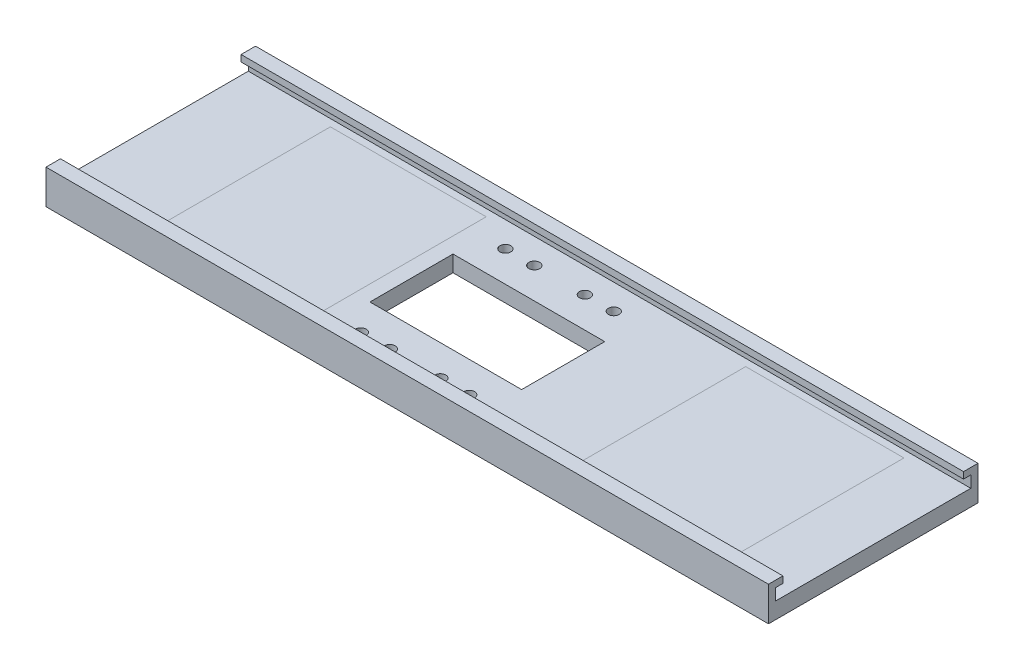
SolidWorks part; units mm, degrees
ref_plane "前视基准面" through (0, 0, 0) normal (0, 0, 1) x (1, 0, 0)
ref_plane "上视基准面" through (0, 0, 0) normal (0, 1, 0) x (1, 0, 0)
ref_plane "右视基准面" through (0, 0, 0) normal (1, 0, 0) x (0, 0, -1)
sketch "草图1" plane through (0, 0, 0) normal (1, 0, 0) x (0, 0, -1)
  line L0 (0, 28.6691) -> (0, -27.5601) construction
  line L1 (-29, 0) -> (29, 0)
  line L2 (29, 0) -> (29, 9.5)
  line L3 (29, 9.5) -> (25, 9.5)
  line L4 (25, 9.5) -> (25, 4.5)
  line L5 (25, 4.5) -> (-25, 4.5)
  line L6 (-29, 0) -> (-29, 9.5)
  line L7 (-29, 9.5) -> (-25, 9.5)
  line L8 (-25, 9.5) -> (-25, 4.5)
  point P10 (0, 0)
  point P13 (0, 4.5)
  dimension "D1" = 50
  dimension "D2" = 4.5
  dimension "D3" = 4
  dimension "D4" = 5
extrude "凸台-拉伸1" add sketch "草图1" along normal blind 180 and the other way blind 20
sketch "草图2" plane through (0, 4.5, 0) normal (0, 1, 0) x (1, 0, 0)
  line L0 (0, 0) -> (180, 0) construction
  line L1 (180, 25) -> (180, -25) construction
  line L2 (75, 10) -> (75, -10) construction
  line L5 (58.67, 10) -> (58.67, -10) construction
  line L8 (97.67, 10) -> (97.67, -10) construction
  line L9 (58.67, 10) -> (97.67, 10) construction
  line L10 (58.67, -10) -> (97.67, -10) construction
  line L20 (52.17, 11.5) -> (94.17, 11.5)
  line L21 (52.17, 11.5) -> (52.17, -11.5)
  line L22 (52.17, -11.5) -> (94.17, -11.5)
  line L23 (94.17, 11.5) -> (94.17, -11.5)
  line L24 (52.17, 11.5) -> (94.17, -11.5) construction
  line L25 (52.17, -11.5) -> (94.17, 11.5) construction
  circle A0 centre (90, 0) radius 3 construction
  point P6 (63.3128, 0)
  point P7 (73.17, 0)
  dimension "D1" = 6
  dimension "D2" = 31.33
  dimension "D3" = 39
  dimension "D4" = 10
  dimension "D5" = 10
  dimension "D6" = 23
  dimension "D7" = 42
extrude "切除-拉伸1" cut sketch "草图2" against normal through all
sketch "草图4" plane through (0, 4.5, 0) normal (0, 1, 0) x (1, 0, 0)
  line L1 (73.17, 25) -> (73.17, -25) construction
  line L2 (-20, 25) -> (180, 25) construction
  line L3 (-20, -25) -> (180, -25) construction
  line L7 (94.17, 11.5) -> (52.17, 11.5) construction
  line L8 (-20, 25) -> (180, 25) construction
  line L9 (-20, 0) -> (180, 0) construction
  line L10 (-20, 25) -> (-20, -25) construction
  line L11 (180, 25) -> (180, -25) construction
  circle A8 centre (66.17, 20) radius 1.5
  circle A9 centre (80.17, 20) radius 1.5
  circle A10 centre (88.17, 20) radius 1.5
  circle A11 centre (58.17, 20) radius 1.5
  circle A12 centre (88.17, -20) radius 1.5
  circle A13 centre (80.17, -20) radius 1.5
  circle A14 centre (66.17, -20) radius 1.5
  circle A15 centre (58.17, -20) radius 1.5
  point P13 (73.17, 11.5)
  dimension "D1" = 3
  dimension "D2" = 5
  dimension "D6" = 5
  dimension "D4" = 3
  dimension "D3" = 14
  dimension "D5" = 8
extrude "切除-拉伸2" cut sketch "草图4" against normal through all
ref_plane "基准面1" through (180, 0, 0) normal (1, 0, 0) x (0, 0, -1)
sketch "草图5" plane through (180, 0, 0) normal (1, 0, 0) x (0, 0, -1)
  line L1 (-25, 4.5) -> (-25, 9.5) construction
  line L3 (-25, 7.7) -> (-25, 5.5)
  line L8 (-25, 7.7) -> (-27, 7.7)
  line L9 (-27, 7.7) -> (-27, 5.5)
  line L10 (-27, 5.5) -> (-25, 5.5)
  line L11 (0, 10.1018) -> (0, 0) construction
  line L12 (25, 7.7) -> (25, 5.5)
  line L13 (27, 5.5) -> (25, 5.5)
  line L14 (27, 7.7) -> (27, 5.5)
  line L15 (25, 7.7) -> (27, 7.7)
  dimension "D1" = 1
  dimension "D2" = 2
  dimension "D3" = 2.2
extrude "切除-拉伸3" cut sketch "草图5" against normal blind 225
ref_plane "基准面2" through (0, 0, 0) normal (0, -1, 0) x (-1, 0, 0)
sketch "草图6" plane through (0, 0, 0) normal (0, -1, 0) x (-1, 0, 0)
  line L0 (-94.17, 0) -> (-52.17, 0) construction
  line L1 (-94.17, -11.5) -> (-94.17, 11.5) construction
  line L2 (-52.17, 11.5) -> (-52.17, -11.5) construction
  line L3 (-73.17, -11.5) -> (-73.17, 11.5) construction
  line L4 (-52.17, -11.5) -> (-94.17, -11.5) construction
  line L5 (-94.17, 11.5) -> (-52.17, 11.5) construction
  circle A0 centre (-97.93, 5) radius 3
  circle A1 centre (-48.41, 5) radius 3
  circle A2 centre (-48.41, -5) radius 3
  circle A3 centre (-97.93, -5) radius 3
  dimension "D2" = 6
  dimension "D1" = 24.76
  dimension "D3" = 5
extrude "切除-拉伸4" cut sketch "草图6" against normal blind 3.5
sketch "草图7" plane through (180, 0, 0) normal (1, 0, 0) x (0, 0, -1)
  line L0 (-27, 5.5) -> (-25, 5.5)
  line L1 (-25, 5.5) -> (-25, 4.5)
  line L2 (-25, 4.5) -> (-27, 4.5)
  line L3 (-27, 4.5) -> (-27, 5.5)
  line L4 (0, 5.225) -> (0, -5.225) construction
  line L5 (25, 4.5) -> (27, 4.5)
  line L6 (25, 5.5) -> (25, 4.5)
  line L7 (27, 5.5) -> (25, 5.5)
  line L8 (27, 4.5) -> (27, 5.5)
extrude "切除-拉伸5" cut sketch "草图7" against normal blind 200
sketch "草图8" plane through (0, 4.5, 0) normal (0, 1, 0) x (1, 0, 0)
  line L1 (4.7038, 25.0184) -> (47.8408, 25.0184)
  line L2 (4.7038, 25.0184) -> (4.7038, -25.1527)
  line L3 (4.7038, -25.1527) -> (47.8408, -25.1527)
  line L4 (47.8408, 25.0184) -> (47.8408, -25.1527)
  line L5 (119.6714, 25.0184) -> (163.4776, 25.0184)
  line L6 (119.6714, 25.0184) -> (119.6714, -25.1527)
  line L7 (119.6714, -25.1527) -> (163.4776, -25.1527)
  line L8 (163.4776, 25.0184) -> (163.4776, -25.1527)
split line "分割线1"
